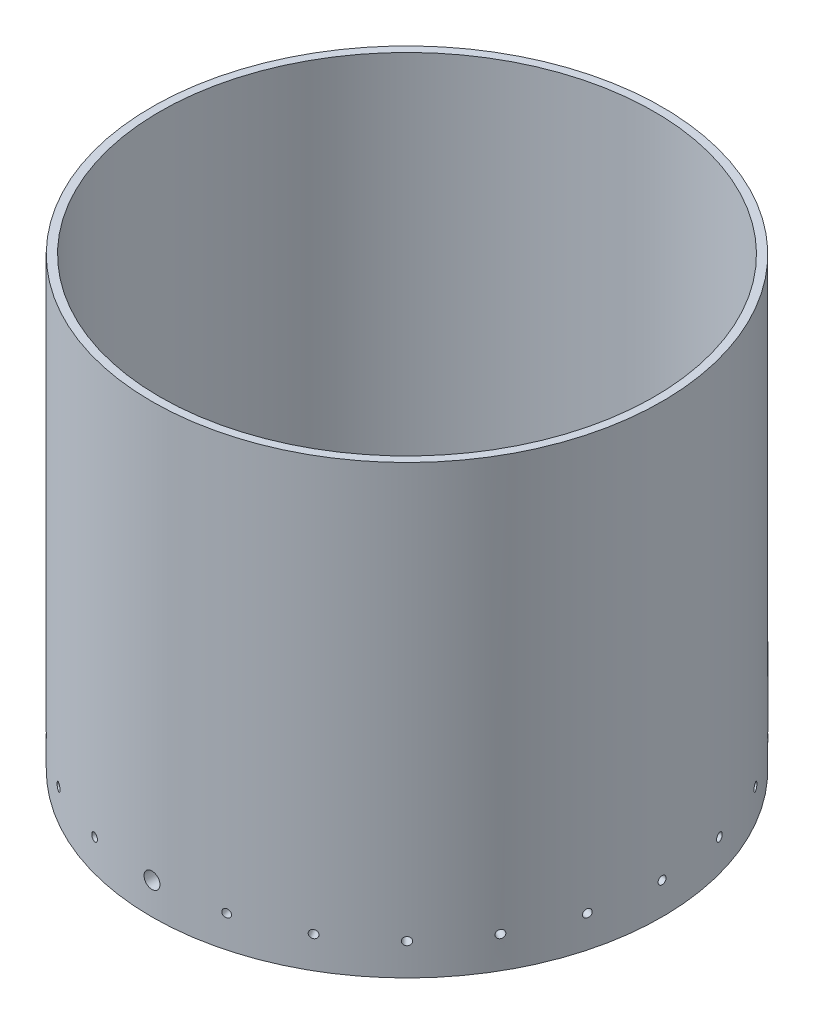
SolidWorks part; units mm, degrees
ref_plane "Front Plane" through (0, 0, 0) normal (0, 0, 1) x (1, 0, 0)
ref_plane "Top Plane" through (0, 0, 0) normal (0, 1, 0) x (1, 0, 0)
ref_plane "Right Plane" through (0, 0, 0) normal (1, 0, 0) x (0, 0, -1)
sketch "Sketch1" plane through (0, 0, 0) normal (0, 1, 0) x (1, 0, 0)
  circle A0 centre (0, 0) radius 101.6
  circle A1 centre (0, 0) radius 95.25
  dimension "D1" = 203.2
  dimension "D2" = 190.5
extrude "Boss-Extrude1" add sketch "Sketch1" along normal blind 25.4
sketch "Sketch2" plane through (0, 0, 0) normal (0, 0, 1) x (1, 0, 0)
  circle A0 centre (0, 12.7) radius 3.175
  dimension "D1" = 6.35
extrude "Cut-Extrude1" cut sketch "Sketch2" against normal through all and the other way through all
sketch "Sketch3" plane through (0, 0, 0) normal (1, 0, 0) x (0, 0, -1)
  circle A0 centre (0, 12.7) radius 1.5875
  dimension "D1" = 3.175
extrude "Cut-Extrude3" cut sketch "Sketch3" against normal through all
sketch "Sketch4" plane through (0, 0, 0) normal (1, 0, 0) x (0, 0, -1)
  line L0 (0, 0) -> (0, 72.5565) construction
pattern_circular "CirPattern1" count 24 over 360 about axis through (0, 0, 0) along (0, 1, 0) of "Cut-Extrude3"
sketch "Sketch5" plane through (0, 25.4, 0) normal (0, 1, 0) x (1, 0, 0)
  circle A0 centre (0, 0) radius 98.425
  circle A1 centre (0, 0) radius 101.6
extrude "Boss-Extrude2" add sketch "Sketch5" along normal blind 152.4
